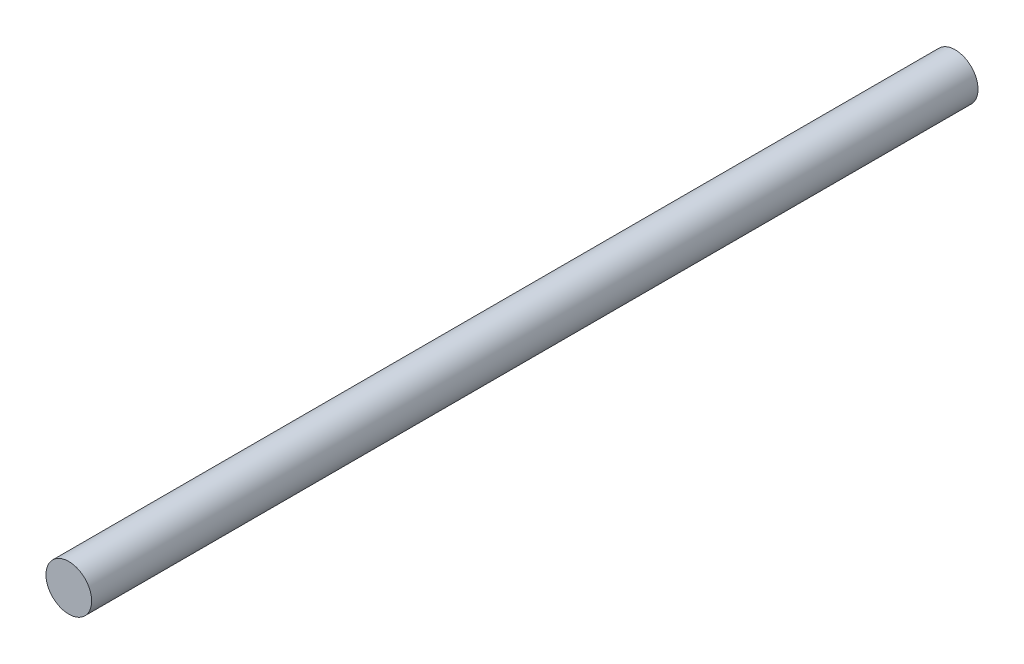
SolidWorks part; units mm, degrees
ref_plane "Front Plane" through (0, 0, 0) normal (0, 0, 1) x (1, 0, 0)
ref_plane "Top Plane" through (0, 0, 0) normal (0, 1, 0) x (1, 0, 0)
ref_plane "Right Plane" through (0, 0, 0) normal (1, 0, 0) x (0, 0, -1)
sketch "Sketch1" plane through (0, 0, 0) normal (0, 0, 1) x (1, 0, 0)
  circle A0 centre (0, 0) radius 2.5
  dimension "D1" = 5
extrude "Boss-Extrude1" add sketch "Sketch1" along normal blind 97
